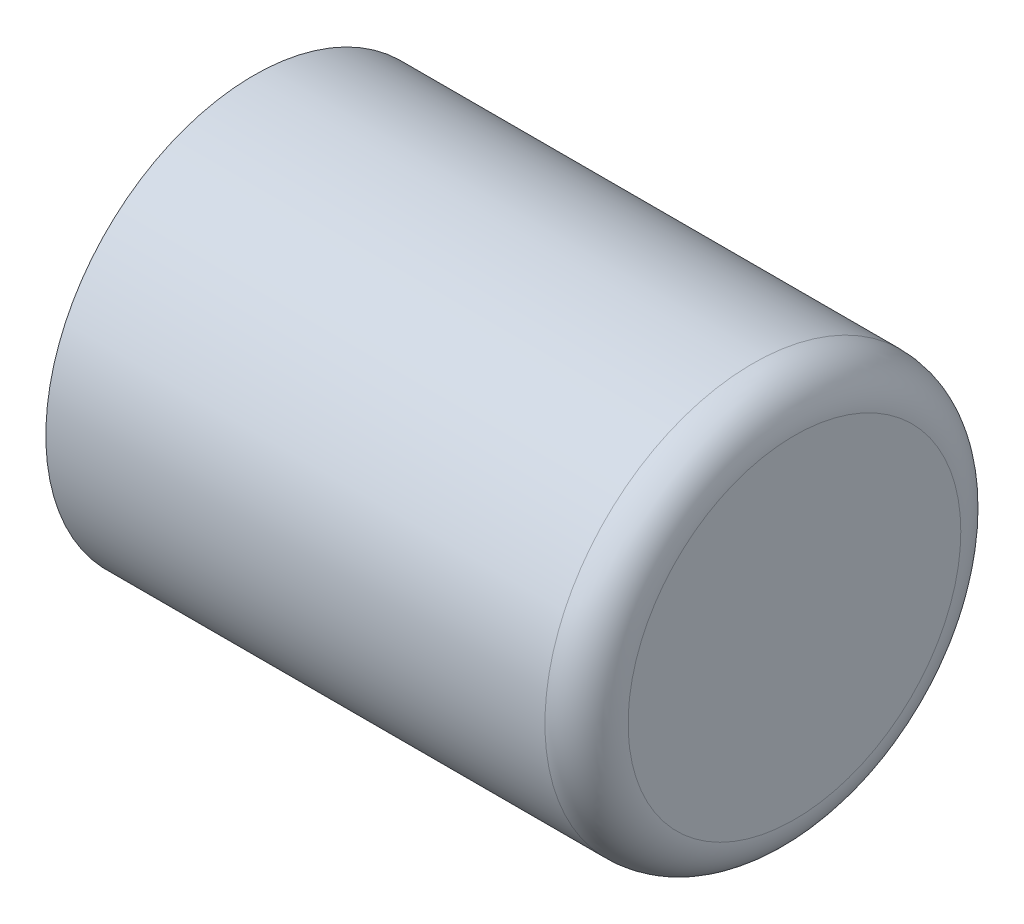
SolidWorks part; units mm, degrees
ref_plane "Front Plane" through (0, 0, 0) normal (0, 0, 1) x (1, 0, 0)
ref_plane "Top Plane" through (0, 0, 0) normal (0, 1, 0) x (1, 0, 0)
ref_plane "Right Plane" through (0, 0, 0) normal (1, 0, 0) x (0, 0, -1)
sketch "Sketch1" plane through (0, 0, 0) normal (1, 0, 0) x (0, 0, -1)
  circle A0 centre (0, 0) radius 5
  circle A1 centre (0, 0) radius 2.5
  dimension "D1" = 10
  dimension "D2" = 5
extrude "Boss-Extrude1" add sketch "Sketch1" along normal blind 12
sketch "Sketch2" plane through (12, 0, 0) normal (1, 0, 0) x (0, 0, -1)
  circle A0 centre (0, 0) radius 5
  dimension "D1" = 10
extrude "Boss-Extrude2" add sketch "Sketch2" along normal blind 1
fillet "Fillet1" radius 1 1 edges at (13, 0, -5)
sketch "Sketch3" plane through (0, 0, 0) normal (-1, 0, 0) x (0, 0, 1)
  line L0 (0, -5) -> (0, 5) construction
  line L1 (-5, 0) -> (5, 0) construction
  circle A0 centre (0, 0) radius 5 construction
  point P7 (0, 0)
sketch "Sketch4" plane through (0, 0, 0) normal (0, 0, 1) x (1, 0, 0)
  line L0 (0, 0) -> (-31.717, 0) construction
  line L1 (-31.717, 0) -> (-31.717, -5.8662) construction
